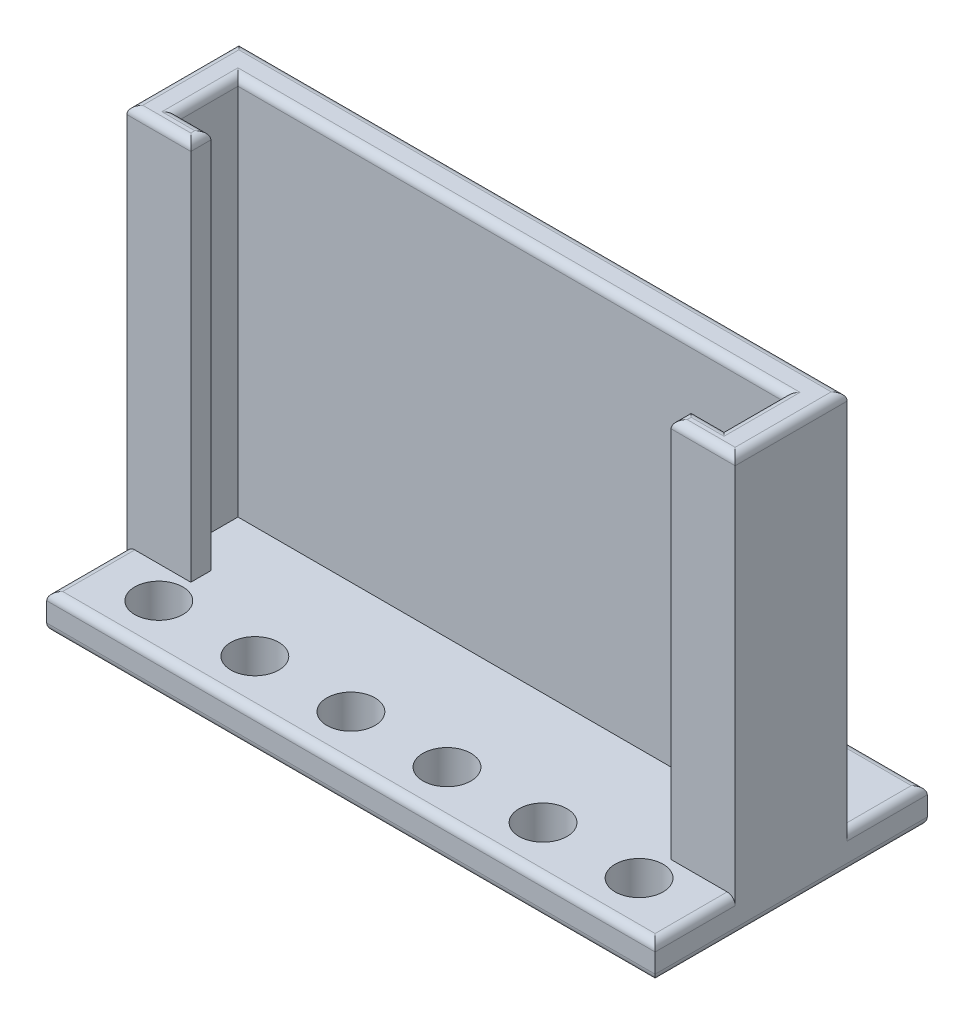
SolidWorks part; units mm, degrees
material "Copper"
ref_plane "Front Plane" through (0, 0, 0) normal (0, 0, 1) x (1, 0, 0)
ref_plane "Top Plane" through (0, 0, 0) normal (0, 1, 0) x (1, 0, 0)
ref_plane "Right Plane" through (0, 0, 0) normal (1, 0, 0) x (0, 0, -1)
sketch "Sketch2" plane through (0, 0, 0) normal (0, 0, 1) x (1, 0, 0)
  line L1 (0, 0) -> (96.52, 0)
  line L2 (0, 0) -> (0, 66.04)
  line L3 (0, 66.04) -> (96.52, 66.04)
  line L4 (96.52, 0) -> (96.52, 66.04)
  dimension "D1" = 96.52
  dimension "D2" = 66.04
extrude "Boss-Extrude1" add sketch "Sketch2" along normal blind 17.78
sketch "Sketch3" plane through (0, 0, 17.78) normal (0, 0, 1) x (1, 0, 0)
  line L0 (96.52, 0) -> (96.52, 66.04) construction
  line L1 (0, 0) -> (96.52, 0)
  line L2 (0, 0) -> (0, 5.588)
  line L3 (0, 5.588) -> (96.52, 5.588)
  line L4 (96.52, 0) -> (96.52, 5.588)
  dimension "D1" = 5.588
extrude "Boss-Extrude2" add sketch "Sketch3" along normal blind 12.7
sketch "Sketch4" plane through (0, 66.04, 0) normal (0, 1, 0) x (1, 0, 0)
  line L5 (0, -5.08) -> (4.9403, -5.08) construction
  line L6 (0, -17.78) -> (0, 0) construction
  line L7 (96.52, -17.78) -> (96.52, 0) construction
  line L8 (0, -14.605) -> (4.9403, -14.605) construction
  line L9 (4.9403, -5.08) -> (91.5797, -5.08)
  line L10 (4.9403, -5.08) -> (4.9403, -14.605)
  line L11 (4.9403, -14.605) -> (91.5797, -14.605)
  line L12 (91.5797, -5.08) -> (91.5797, -14.605)
  line L13 (91.5797, -14.605) -> (96.52, -14.605) construction
  line L14 (91.5797, -5.08) -> (96.52, -5.08) construction
  line L15 (96.52, -17.78) -> (0, -17.78) construction
  line L16 (10.16, -14.605) -> (86.36, -14.605)
  line L17 (10.16, -14.605) -> (10.16, -17.78)
  line L18 (10.16, -17.78) -> (86.36, -17.78)
  line L19 (86.36, -14.605) -> (86.36, -17.78)
  point P18 (48.26, -5.08)
  point P19 (48.26, -17.78)
  dimension "D1" = 86.6394
  dimension "D2" = 9.525
  dimension "D3" = 3.175
  dimension "D4" = 76.2
extrude "Cut-Extrude1" cut sketch "Sketch4" against normal up to surface (60.452 mm away) contours L12 L9 L10 L11 | L18 L19 L16 L17 up to face at (48.26, 5.588, 24.13)
sketch "Sketch5" plane through (0, 0, 0) normal (0, 0, -1) x (-1, 0, 0)
  line L0 (0, 66.04) -> (0, 0) construction
  line L1 (-96.52, 0) -> (0, 0)
  line L2 (-96.52, 0) -> (-96.52, 5.588)
  line L3 (-96.52, 5.588) -> (0, 5.588)
  line L4 (0, 0) -> (0, 5.588)
  dimension "D1" = 5.588
extrude "Boss-Extrude3" add sketch "Sketch5" along normal blind 12.7
sketch "Sketch6" plane through (0, 5.588, 0) normal (0, 1, 0) x (1, 0, 0)
  line L0 (96.52, -22.86) -> (86.36, -22.86) construction
  line L3 (96.52, 6.35) -> (86.36, 6.35) construction
  line L4 (96.52, 12.7) -> (96.52, 0) construction
  line L5 (0, 12.7) -> (0, 0) construction
  line L6 (86.36, 6.35) -> (10.16, 6.35) construction
  line L7 (10.16, 6.35) -> (0, 6.35) construction
  line L8 (10.16, -22.86) -> (0, -22.86) construction
  line L9 (96.52, -30.48) -> (96.52, -17.78) construction
  line L10 (0, -30.48) -> (0, -17.78) construction
  circle A0 centre (10.16, 6.35) radius 2.413
  circle A1 centre (22.86, 6.35) radius 2.413
  circle A2 centre (35.56, 6.35) radius 2.413
  circle A3 centre (48.26, 6.35) radius 2.413
  circle A4 centre (60.96, 6.35) radius 2.413
  circle A5 centre (73.66, 6.35) radius 2.413
  circle A6 centre (86.36, 6.35) radius 2.413
  circle A7 centre (10.16, -22.86) radius 3.81
  circle A8 centre (25.4, -22.86) radius 3.81
  circle A9 centre (40.64, -22.86) radius 3.81
  circle A10 centre (55.88, -22.86) radius 3.81
  circle A11 centre (71.12, -22.86) radius 3.81
  circle A12 centre (86.36, -22.86) radius 3.81
  dimension "D1" = 4.826
  dimension "D4" = 7.62
  dimension "D3" = 12.7
  dimension "D6" = 15.24
  dimension "D7" = 5.08
  dimension "D2" = 7
  dimension "D5" = 6
extrude "Cut-Extrude2" cut sketch "Sketch6" against normal through all
fillet "Fillet1" radius 1.27 12 edges at (88.9698, 66.04, 14.605) (91.5797, 66.04, 9.8425) (48.26, 66.04, 5.08) (4.9403, 66.04, 9.8425) (7.5501, 66.04, 14.605) (10.16, 66.04, 16.1925) (5.08, 66.04, 17.78) (0, 66.04, 8.89) (48.26, 66.04, 0) (96.52, 66.04, 8.89) (91.44, 66.04, 17.78) (86.36, 66.04, 16.1925)
fillet "Fillet2" radius 1.27 6 edges at (96.52, 5.588, -6.35) (48.26, 5.588, -12.7) (0, 5.588, -6.35) (96.52, 5.588, 24.13) (48.26, 5.588, 30.48) (0, 5.588, 24.13)
fillet "Fillet3" radius 1.27 4 edges at (48.26, 0, -12.7) (96.52, 0, 8.89) (48.26, 0, 30.48) (0, 0, 8.89)
